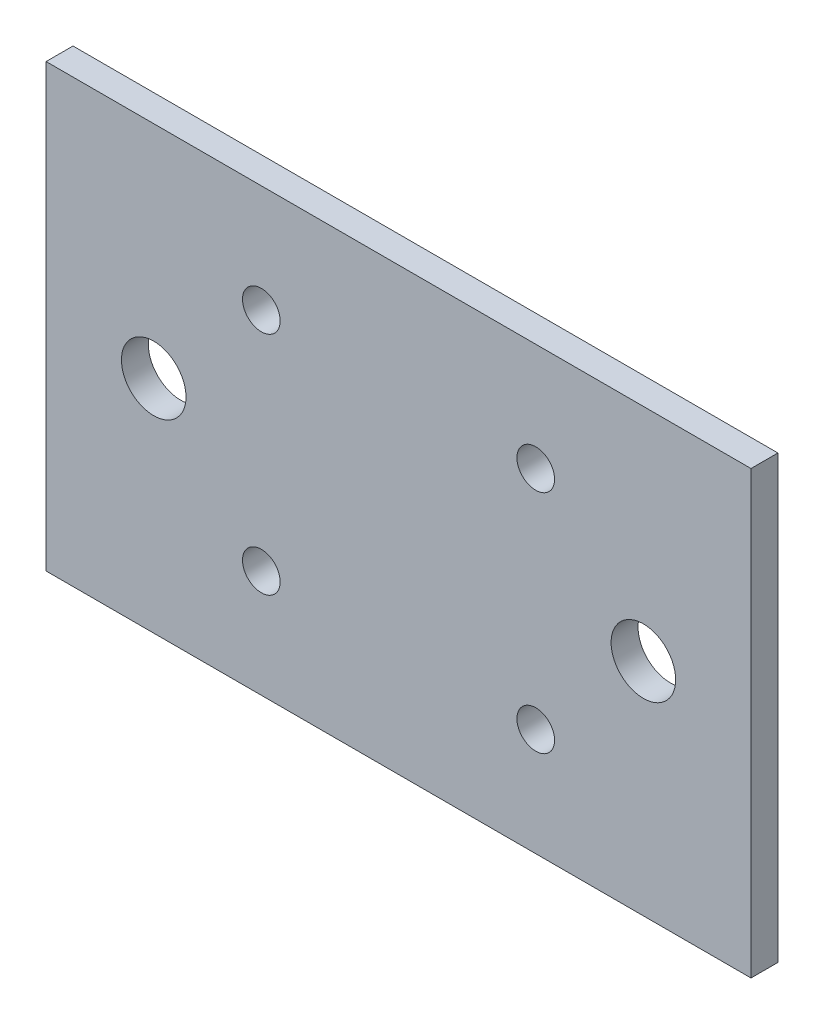
SolidWorks part; units mm, degrees
ref_plane "Front Plane" through (0, 0, 0) normal (0, 0, 1) x (1, 0, 0)
ref_plane "Top Plane" through (0, 0, 0) normal (0, 1, 0) x (1, 0, 0)
ref_plane "Right Plane" through (0, 0, 0) normal (1, 0, 0) x (0, 0, -1)
sketch "Sketch1" plane through (0, 0, 0) normal (0, 0, 1) x (1, 0, 0)
  line L0 (-22.75, 0) -> (22.75, 0) construction
  line L1 (-32.75, 20.5) -> (32.75, 20.5)
  line L2 (-32.75, 20.5) -> (-32.75, -20.5)
  line L3 (-32.75, -20.5) -> (32.75, -20.5)
  line L4 (32.75, 20.5) -> (32.75, -20.5)
  line L5 (-32.75, 20.5) -> (32.75, -20.5) construction
  line L6 (-32.75, -20.5) -> (32.75, 20.5) construction
  line L8 (-12.75, -10.5) -> (12.75, -10.5) construction
  line L9 (-12.75, -10.5) -> (-12.75, 10.5) construction
  line L10 (-12.75, 10.5) -> (12.75, 10.5) construction
  line L11 (12.75, -10.5) -> (12.75, 10.5) construction
  line L12 (-12.75, -10.5) -> (12.75, 10.5) construction
  line L13 (-12.75, 10.5) -> (12.75, -10.5) construction
  circle A0 centre (-22.75, 0) radius 3
  circle A1 centre (22.75, 0) radius 3
  circle A2 centre (-12.75, 10.5) radius 1.75
  circle A3 centre (12.75, 10.5) radius 1.75
  circle A4 centre (12.75, -10.5) radius 1.75
  circle A5 centre (-12.75, -10.5) radius 1.75
  point P0 (0, 0)
  point P10 (0, 0)
  dimension "D2" = 6
  dimension "D7" = 3.5
  dimension "D1" = 10
  dimension "D3" = 21
  dimension "D4" = 25.5
  dimension "D5" = 20
  dimension "D6" = 10
extrude "Boss-Extrude1" add sketch "Sketch1" along normal blind 2.5
